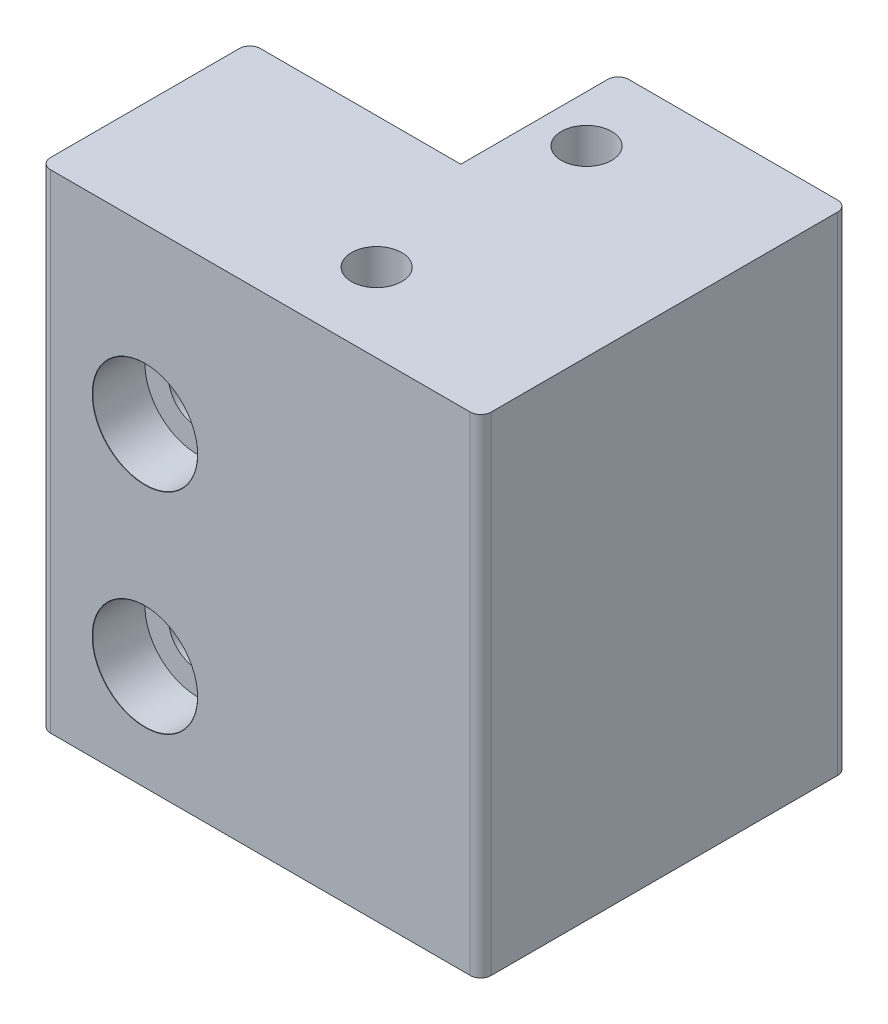
SolidWorks part; units mm, degrees
ref_plane "Front Plane" through (0, 0, 0) normal (0, 0, 1) x (1, 0, 0)
ref_plane "Top Plane" through (0, 0, 0) normal (0, 1, 0) x (1, 0, 0)
ref_plane "Right Plane" through (0, 0, 0) normal (1, 0, 0) x (0, 0, -1)
sketch "Sketch1" plane through (0, 0, 0) normal (0, 1, 0) x (1, 0, 0)
  line L1 (21, 10) -> (-21, 10)
  line L2 (21, 10) -> (21, -10)
  line L3 (21, -10) -> (-21, -10)
  line L4 (-21, 10) -> (-21, -10)
  line L5 (21, 10) -> (-21, -10) construction
  line L6 (21, -10) -> (-21, 10) construction
  point P0 (0, 0)
  dimension "D1" = 42
  dimension "D2" = 20
extrude "Boss-Extrude1" add sketch "Sketch1" along normal blind 40
sketch "Sketch2" plane through (0, 40, 0) normal (0, 1, 0) x (1, 0, 0)
  line L0 (-21, 10) -> (-21, -10) construction
  line L1 (21, 10) -> (-0.9, 10)
  line L2 (21, 10) -> (21, 25)
  line L3 (21, 25) -> (-0.9, 25)
  line L4 (-0.9, 10) -> (-0.9, 25)
  dimension "D1" = 15
  dimension "D2" = 20.1
extrude "Boss-Extrude2" add sketch "Sketch2" against normal up to surface (40 mm away) up to face at (0, 0, 0)
sketch "Sketch3" plane through (0, 0, 10) normal (0, 0, 1) x (1, 0, 0)
  line L0 (-21, 20) -> (21, 20) construction
  line L1 (-21, 40) -> (-21, 0) construction
  line L2 (21, 40) -> (21, 0) construction
  line L3 (-11, 30) -> (-11, 10)
  point P9 (-11, 20)
  dimension "D1" = 20
  dimension "D2" = 10
hole_wizard "CBORE for M5 SHCS1" positions "Sketch4" profile "Sketch5" counterbore size "M5" standard "ANSI Metric" end condition through all
sketch "Sketch4" plane through (0, 0, 10) normal (0, 0, 1) x (1, 0, 0)
  point P0 (-11, 30)
  point P3 (-11, 10)
sketch "Sketch5" plane through (-11, 30, 10) normal (1, 0, 0) x (0, -1, 0)
  line L0 (0, 0) -> (0, 35)
  line L1 (0, 35) -> (2.75, 35)
  line L3 (2.75, 35) -> (2.75, 5)
  line L4 (5, 5) -> (2.75, 5)
  line L5 (5, 5) -> (5, 0.021)
  line L6 (5, 0.021) -> (5.025, 0)
  line L7 (5.025, 0) -> (0, 0)
  line L8 (-5, 0.021) -> (-5.025, 0) construction
  line L11 (0, -6.35) -> (0, 107.95) construction
  dimension "Thru Hole Dia." = 5.5
  dimension "Thru Hole Depth" = 35
  dimension "C'Bore Dia." = 10
  dimension "C'Bore Depth" = 5
  dimension "Near C'Sink Dia." = 10.05
  dimension "Near C'Sink Angle" = 100
sketch "Sketch6" plane through (0, 40, 0) normal (0, 1, 0) x (1, 0, 0)
  line L6 (-21, 10) -> (-21, -10)
  line L7 (-21, -10) -> (21, -10)
  line L8 (21, -10) -> (21, 25)
  line L9 (21, 25) -> (-0.9, 25)
  line L10 (-0.9, 25) -> (-0.9, 10)
  line L11 (-0.9, 10) -> (-21, 10)
  line L12 (-21, 10) -> (-21, -10)
  line L13 (-21, -10) -> (21, -10)
  line L14 (21, -10) -> (21, 25)
  line L15 (21, 25) -> (-0.9, 25)
  line L16 (-0.9, 25) -> (-0.9, 10)
  line L17 (-0.9, 10) -> (-21, 10)
  dimension "D1" = 0
extrude "Boss-Extrude3" add sketch "Sketch6" along normal blind 6.5
sketch "Sketch7" plane through (0, 46.5, 0) normal (0, 1, 0) x (1, 0, 0)
  line L0 (16.51, 25) -> (16.51, -2.5123)
  line L1 (21, 25) -> (-0.9, 25) construction
  line L2 (21, -10) -> (21, 25) construction
  dimension "D1" = 4.49
fillet "Fillet1" radius 1 5 edges at (-0.9, 23.25, -25) (21, 23.25, -25) (21, 23.25, 10) (-21, 23.25, -10) (-21, 23.25, 10)
sketch "Sketch8" plane through (0, 46.5, 0) normal (0, 1, 0) x (1, 0, 0)
  line L0 (3.58, 25) -> (3.58, -10) construction
  line L1 (20, 25) -> (0.1, 25) construction
  line L2 (-20, -10) -> (20, -10) construction
  line L3 (-21, 9) -> (-21, -9) construction
  line L4 (3.58, 17.5) -> (3.58, -2.5) construction
  circle A0 centre (3.58, 17.5) radius 2.4
  circle A1 centre (3.58, -2.5) radius 2.4
  point P11 (3.58, 7.5)
  dimension "D3" = 4.8
  dimension "D1" = 24.58
  dimension "D2" = 20
extrude "Cut-Extrude1" cut sketch "Sketch8" against normal blind 3.8
sketch "Sketch9" plane through (0, 42.7, 0) normal (0, 1, 0) x (1, 0, 0)
  circle A0 centre (3.58, 17.5) radius 1.65
  circle A1 centre (3.58, -2.5) radius 1.65
  point P0 (3.58, 17.5)
  point P1 (3.58, -2.5)
  dimension "D1" = 3.3
extrude "Cut-Extrude2" cut sketch "Sketch9" against normal blind 3
